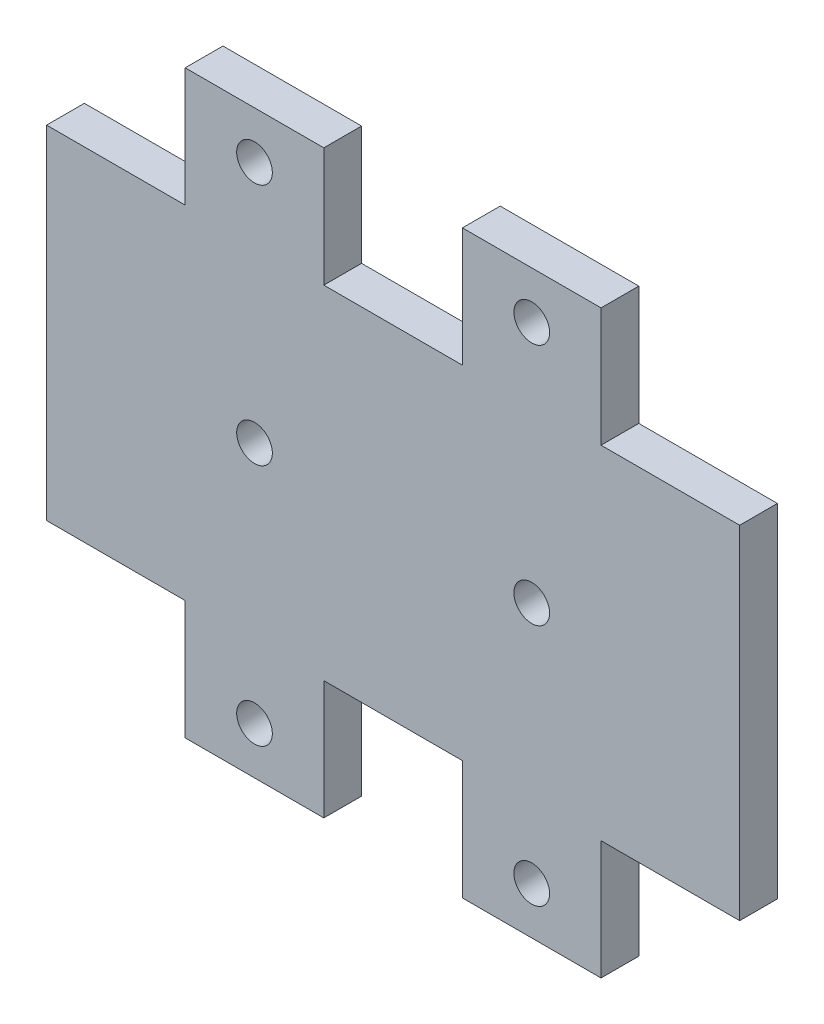
SolidWorks part; units mm, degrees
ref_plane "Front Plane" through (0, 0, 0) normal (0, 0, 1) x (1, 0, 0)
ref_plane "Top Plane" through (0, 0, 0) normal (0, 1, 0) x (1, 0, 0)
ref_plane "Right Plane" through (0, 0, 0) normal (1, 0, 0) x (0, 0, -1)
sketch "Sketch2" plane through (0, 0, 0) normal (0, 0, 1) x (1, 0, 0)
  line L0 (23.312, 14.4) -> (29.14, 14.4)
  line L2 (0, 0) -> (0, 14.4)
  line L3 (0, 14.4) -> (11.656, 14.4)
  line L24 (11.656, 14.4) -> (11.656, 24.4)
  line L25 (11.656, 24.4) -> (23.312, 24.4)
  line L26 (23.312, 14.4) -> (23.312, 24.4)
  line L28 (29.14, 14.4) -> (29.14, 0)
  line L29 (0, 0) -> (15.985, 0)
  line L30 (18.985, 0) -> (29.14, 0)
  circle A1 centre (17.484, 20.4312) radius 1.5
  arc A2 (18.985, 0) -> (15.985, 0) centre (17.485, 0) ccw
  point P4 (0, 0)
  dimension "D4" = 11.656
  dimension "D13" = 5.828
  dimension "D3" = 3
  dimension "D10" = 3
  dimension "D2" = 5.828
  dimension "D5" = 14.4
  dimension "D6" = 11.655
  dimension "D9" = 3.9688
  dimension "D11" = 11.656
  dimension "D12" = 10
extrude "Boss-Extrude1" add sketch "Sketch2" along normal blind 3.175
mirror "Mirror1" about plane through (0, 0, 3.175) normal (0, 1, 0) of bodies 101
mirror "Mirror2" about plane through (29.14, 14.4, 3.175) normal (-1, 0, 0) of bodies 105
